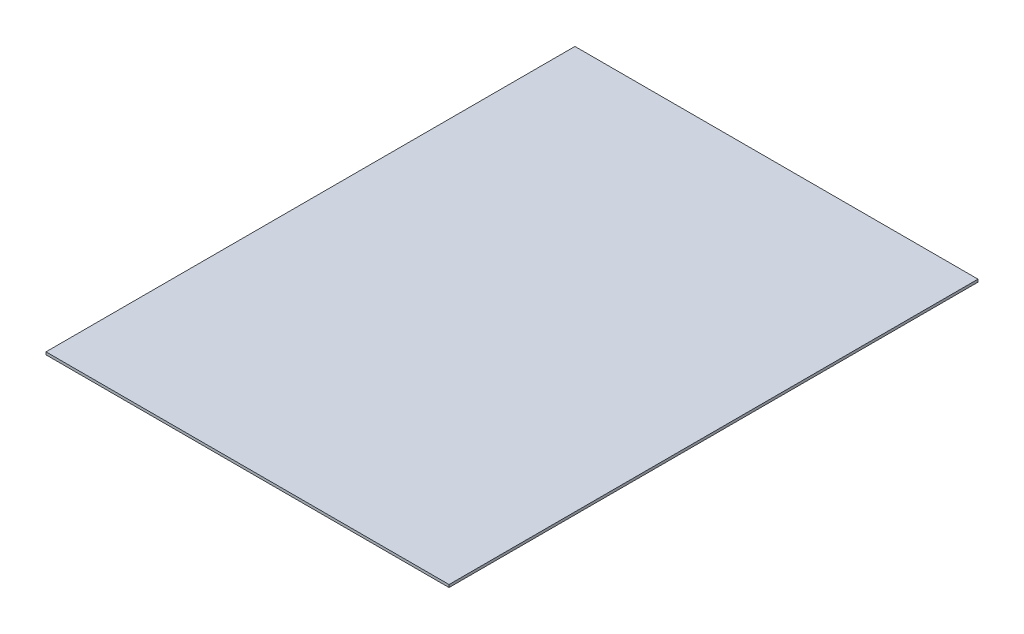
SolidWorks part; units mm, degrees
ref_plane "Front Plane" through (0, 0, 0) normal (0, 0, 1) x (1, 0, 0)
ref_plane "Top Plane" through (0, 0, 0) normal (0, 1, 0) x (1, 0, 0)
ref_plane "Right Plane" through (0, 0, 0) normal (1, 0, 0) x (0, 0, -1)
sketch "Sketch1" plane through (0, 0, 0) normal (0, 1, 0) x (1, 0, 0)
  line L1 (-762, 1000) -> (762, 1000)
  line L2 (-762, 1000) -> (-762, -1000)
  line L3 (-762, -1000) -> (762, -1000)
  line L4 (762, 1000) -> (762, -1000)
  line L5 (-762, 1000) -> (762, -1000) construction
  line L6 (-762, -1000) -> (762, 1000) construction
  point P0 (0, 0)
  dimension "D1" = 2000
  dimension "D2" = 1524
extrude "Boss-Extrude1" add sketch "Sketch1" along normal blind 10
